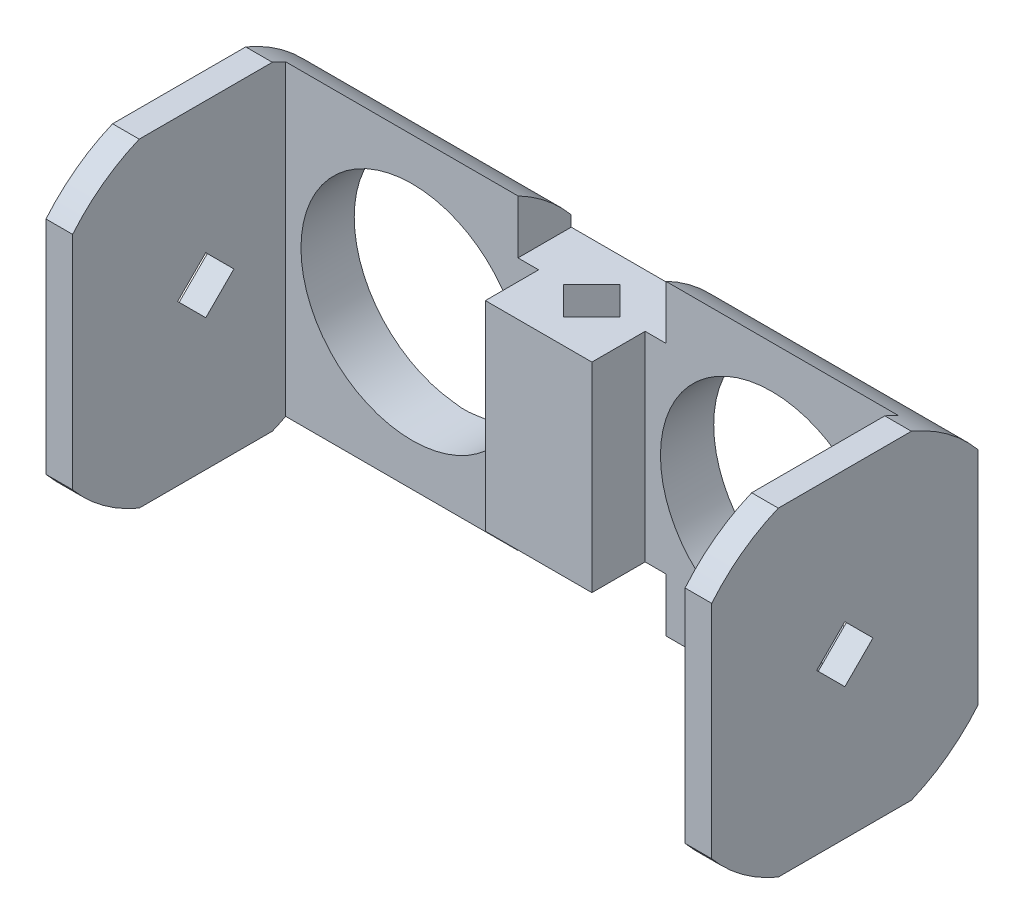
SolidWorks part; units mm, degrees
ref_plane "Plano frontal" through (0, 0, 0) normal (0, 0, 1) x (1, 0, 0)
ref_plane "Plano superior" through (0, 0, 0) normal (0, 1, 0) x (1, 0, 0)
ref_plane "Plano direito" through (0, 0, 0) normal (1, 0, 0) x (0, 0, -1)
sketch "Esboço2" plane through (0, 0, 0) normal (0, 0, 1) x (1, 0, 0)
  line L0 (0, 47.2571) -> (8.5, 47.2571)
  line L1 (0, 47.2571) -> (-8.5, 47.2571)
  line L2 (0, 23.9177) -> (8.5, 23.9177)
  line L3 (0, 23.9177) -> (-8.5, 23.9177)
  line L4 (0, 8.4) -> (0, 75) construction
  line L5 (0, 56.3545) -> (-16, 56.3545) construction
  line L6 (0, 56.3545) -> (16, 56.3545) construction
  line L7 (8.5, 47.2571) -> (8.5, 23.9177)
  line L8 (-8.5, 47.2571) -> (-8.5, 23.9177)
  line L20 (19.3117, 92) -> (-19.3117, 92)
  line L21 (-19.3117, 92) -> (-36.5, 70)
  line L22 (-36.5, 70) -> (-36.5, 0)
  line L23 (-36.5, 0) -> (-22.5, 0)
  line L24 (-22.5, 0) -> (-22.5, 8.4)
  line L25 (-22.5, 8.4) -> (22.5, 8.4)
  line L26 (22.5, 8.4) -> (22.5, 0)
  line L27 (22.5, 0) -> (36.5, 0)
  line L28 (36.5, 0) -> (36.5, 70)
  line L29 (36.5, 70) -> (19.3117, 92)
  circle A8 centre (29.2, 62) radius 2
  circle A9 centre (29.2, 49) radius 2
  circle A10 centre (29.2, 36) radius 2
  circle A11 centre (29.2, 23) radius 2
  circle A12 centre (-29.2, 23) radius 2
  circle A13 centre (0, 75) radius 2
  circle A14 centre (-7, 83.3) radius 2
  circle A15 centre (7, 83.3) radius 2
  circle A16 centre (-29.2, 36) radius 2
  circle A17 centre (-29.2, 49) radius 2
  circle A18 centre (-29.2, 62) radius 2
  circle A20 centre (-29.2, 10) radius 2
  circle A21 centre (29.2, 10) radius 2
  circle A26 centre (-16, 56.3545) radius 2.0867
  circle A27 centre (16, 56.3545) radius 2.0867
  point P31 (0, 23.9177)
  point P33 (0, 47.2571)
sketch "Model" plane through (0, 0, 0) normal (0, 0, 1) x (1, 0, 0)
  line L0 (-13.5, 51.7) -> (0, 51.7) construction
  line L1 (-22.5, 41.7) -> (0, 41.7) construction
  line L2 (0, 50.7729) -> (-23, 50.7729) construction
  line L3 (-22.5, 61.7) -> (-22.5, 41.7) construction
  line L4 (-22.5, 61.7) -> (0, 61.7) construction
  line L5 (-22.5, 61.7) -> (-21, 61.7) construction
  line L6 (-21, 61.7) -> (-21, 43.2) construction
  line L7 (0, 61.7) -> (0, 41.7) construction
  line L8 (0, 61.7) -> (0, 59.2) construction
  line L9 (0, 44.2) -> (0, 59.2)
  line L10 (-23, 63.7) -> (-23, 39.7)
  line L11 (-5.2, 59.2) -> (-0.8, 59.2) construction
  line L12 (-23, 63.7) -> (-5.55, 63.7)
  line L13 (0, 41.7) -> (0, 42.7) construction
  line L14 (-5.55, 63.7) -> (-5.55, 59.2)
  line L15 (0, 42.7) -> (-3.75, 42.7) construction
  line L16 (-3, 57) -> (-3, 61.4) construction
  line L17 (0, 59.2) -> (-5.55, 59.2)
  line L18 (-3, 61.4) -> (0, 61.4) construction
  line L19 (-3, 57) -> (0, 57) construction
  line L20 (-3.75, 41.7) -> (-3.75, 43.7) construction
  line L21 (0, 51.7) -> (-23, 51.7) construction
  line L22 (-3.75, 43.7) -> (0, 43.7) construction
  line L23 (-23, 39.7) -> (-5.55, 39.7)
  line L24 (-3.75, 41.7) -> (-3.75, 34.7) construction
  line L25 (-3.75, 34.7) -> (0, 34.7) construction
  line L26 (-5.55, 39.7) -> (-5.55, 44.2)
  line L27 (0, 44.2) -> (-5.55, 44.2)
  line L34 (-9.5, 39.7) -> (-17.5, 39.7) construction
  line L35 (-17.5, 39.7) -> (-25.5, 47.7) construction
  line L36 (-25.5, 47.7) -> (-25.5, 55.7) construction
  line L37 (-25.5, 55.7) -> (-17.5, 63.7) construction
  line L38 (-17.5, 63.7) -> (-9.5, 63.7) construction
  line L39 (-9.5, 63.7) -> (-5.55, 59.2) construction
  line L40 (-3, 46.75) -> (0, 46.75) construction
  line L41 (-3, 56.65) -> (0, 56.65) construction
  line L42 (-5.55, 44.2) -> (-5.55, 41.2) construction
  line L44 (-2.5, 36.75) -> (-5.55, 41.2) construction
  line L45 (-2.5, 36.75) -> (-2.5, 31.7) construction
  line L48 (-9.5, 31.7) -> (-9.5, 39.7) construction
  line L50 (-2.5, 31.7) -> (-2.5, 29.7) construction
  line L51 (-2.5, 29.7) -> (-9.5, 29.7) construction
  line L52 (-9.5, 29.7) -> (-9.5, 31.7) construction
  line L56 (-36.5, 50.7729) -> (-23.5, 50.7729) construction
  line L57 (-36.5, 70) -> (-36.5, 0) construction
  line L58 (0, 8.4) -> (0, 75) construction
  circle A0 centre (-13.5, 51.7) radius 8.35
  circle A2 centre (-21, 43.2) radius 1 construction
  circle A4 centre (-3, 59.2) radius 2.2 construction
  circle A7 centre (-13.5, 51.7) radius 8 construction
  arc A10 (-5.55, 59.2) -> (-3, 56.65) centre (-3, 59.2) ccw construction
  arc A11 (-3, 46.75) -> (-5.55, 44.2) centre (-3, 44.2) ccw construction
extrude "Ressalto-extrusão2" add sketch "Model" along normal blind 4
sketch "Esboço5" plane through (0, 0, 0) normal (0, 0, -1) x (-1, 0, 0)
  line L1 (23, 63.7) -> (25, 63.7)
  line L2 (23, 63.7) -> (23, 39.7)
  line L3 (23, 39.7) -> (25, 39.7)
  line L4 (25, 63.7) -> (25, 39.7)
extrude "Ressalto-extrusão3" add sketch "Esboço5" against normal blind 20
sketch "Esboço6" plane through (-25, 0, 0) normal (-1, 0, 0) x (0, 0, 1)
  line L0 (0, 51.7) -> (20, 51.7) construction
  line L1 (0, 39.7) -> (0, 63.7) construction
  line L2 (20, 39.7) -> (20, 63.7) construction
  line L3 (20, 51.7) -> (10, 63.7) construction
  line L4 (20, 63.7) -> (0, 63.7) construction
  line L5 (10, 63.7) -> (10, 39.7) construction
  line L6 (20, 39.7) -> (0, 39.7) construction
  circle A0 centre (10, 51.7) radius 13
extrude "Corte-extrusão1" cut sketch "Esboço6" against normal through all flip side to cut
sketch "Esboço8" plane through (-25, 0, 0) normal (-1, 0, 0) x (0, 0, 1)
  line L0 (10, 63.7) -> (10, 39.7) construction
  line L1 (15, 63.7) -> (5, 63.7) construction
  line L2 (15, 39.7) -> (5, 39.7) construction
  line L3 (10, 39.7) -> (0, 51.7) construction
  line L4 (0, 43.3934) -> (0, 60.0066) construction
  line L5 (0, 51.7) -> (20, 51.7) construction
  line L6 (20, 43.3934) -> (20, 60.0066) construction
  line L7 (10, 51.7) -> (7.885, 51.7) construction
  line L8 (10, 51.7) -> (8.5045, 53.1955) construction
  line L9 (10, 51.7) -> (10, 53.815) construction
  line L10 (10, 51.7) -> (11.4955, 53.1955) construction
  line L11 (10, 51.7) -> (12.115, 51.7) construction
  line L12 (10, 51.7) -> (11.4955, 50.2045) construction
  line L13 (10, 51.7) -> (10, 49.585) construction
  line L14 (10, 51.7) -> (8.5045, 50.2045) construction
  line L15 (7.885, 51.7) -> (10, 49.585)
  line L16 (10, 49.585) -> (12.115, 51.7)
  line L17 (12.115, 51.7) -> (10, 53.815)
  line L18 (10, 53.815) -> (7.885, 51.7)
  circle A0 centre (10, 51.7) radius 2.115 construction
  point P24 (10, 51.7)
  dimension "D1" = 8
extrude "Corte-extrusão2" cut sketch "Esboço8" against normal through all
mirror "Espelhar1" about plane through (0, 44.2, 4) normal (-1, 0, 0) of bodies 105
sketch "Esboço9" plane through (0, 0, 4) normal (0, 0, 1) x (1, 0, 0)
  line L0 (0, 59.2) -> (4, 59.2)
  line L1 (5.55, 59.2) -> (-5.55, 59.2) construction
  line L2 (4, 59.2) -> (4, 44.2)
  line L3 (-5.55, 44.2) -> (5.55, 44.2) construction
  line L4 (4, 44.2) -> (-4, 44.2)
  line L5 (-4, 44.2) -> (-4, 59.2)
  line L6 (-4, 59.2) -> (0, 59.2)
extrude "Ressalto-extrusão4" add sketch "Esboço9" along normal blind 4
sketch "Esboço10" plane through (0, 59.2, 0) normal (0, 1, 0) x (1, 0, 0)
  line L0 (0, 0) -> (0, -8) construction
  line L1 (4, -8) -> (-4, -8) construction
  line L2 (0, -4) -> (2.115, -4) construction
  line L3 (0, -4) -> (1.4955, -5.4955) construction
  line L4 (0, -4) -> (0, -6.115) construction
  line L5 (0, -4) -> (-1.4955, -5.4955) construction
  line L6 (0, -4) -> (-2.115, -4) construction
  line L7 (0, -4) -> (-1.4955, -2.5045) construction
  line L8 (0, -4) -> (0, -1.885) construction
  line L9 (0, -4) -> (1.4955, -2.5045) construction
  line L10 (0, -1.885) -> (-2.115, -4)
  line L11 (-2.115, -4) -> (0, -6.115)
  line L12 (0, -6.115) -> (2.115, -4)
  line L13 (2.115, -4) -> (0, -1.885)
  circle A0 centre (0, -4) radius 4.9813 construction
  point P17 (0, -4)
  dimension "D1" = 8
extrude "Corte-extrusão3" cut sketch "Esboço10" against normal through all
